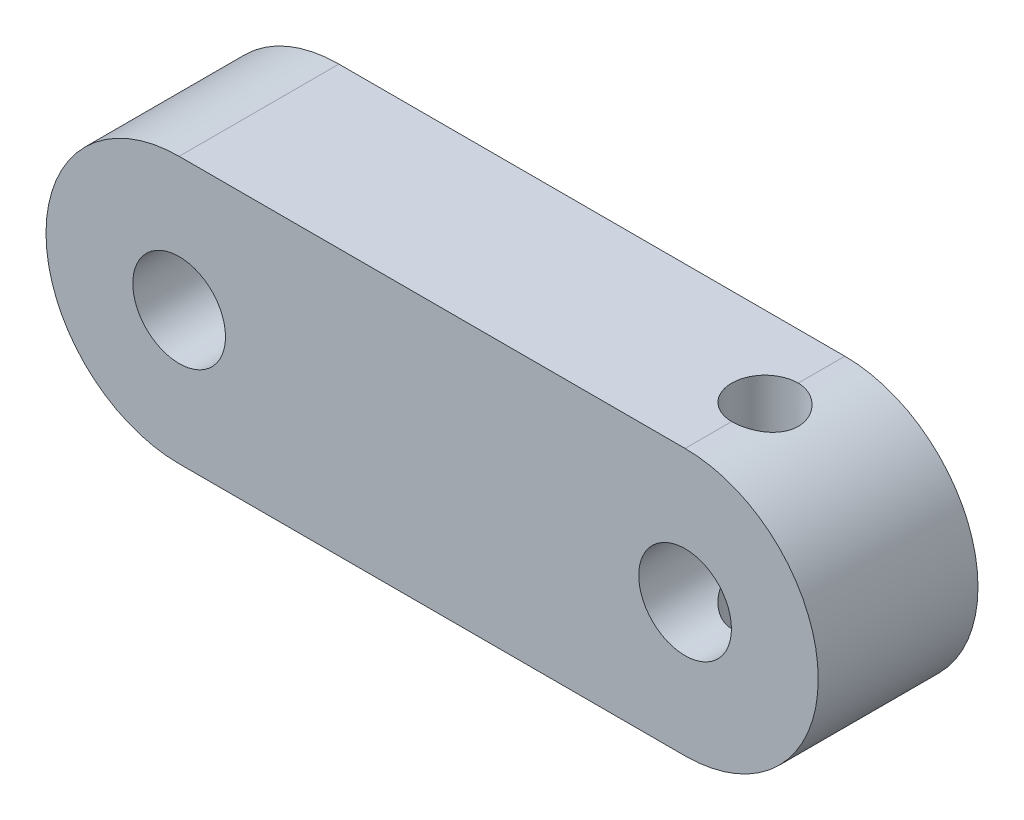
SolidWorks part; units mm, degrees
material "AISI 304"
ref_plane "Front Plane" through (0, 0, 0) normal (0, 0, 1) x (1, 0, 0)
ref_plane "Top Plane" through (0, 0, 0) normal (0, 1, 0) x (1, 0, 0)
ref_plane "Right Plane" through (0, 0, 0) normal (1, 0, 0) x (0, 0, -1)
sketch "Sketch1" plane through (0, 0, 0) normal (0, 0, 1) x (1, 0, 0)
  line L0 (-35.0425, 4.1934) -> (-16.0425, 4.1934)
  line L1 (-35.0425, -5.8066) -> (-16.0425, -5.8066)
  circle A0 centre (-35.0425, -0.8066) radius 1.7407
  circle A1 centre (-16.0425, -0.8066) radius 1.7407
  circle A2 centre (-16.0425, -0.8066) radius 5
  circle A3 centre (-35.0425, -0.8066) radius 5
  dimension "D1" = 19
extrude "Boss-Extrude1" add sketch "Sketch1" along normal blind 6 contours A3 A0 | A3 L1 A2 L0 | A2 A1
sketch "Sketch2" plane through (0, 4.1934, 0) normal (0, 1, 0) x (1, 0, 0)
  line L0 (-16.0425, -6) -> (-16.0425, 0) construction
  circle A0 centre (-16.0425, -3) radius 1.25
extrude "Cut-Extrude1" cut sketch "Sketch2" against normal through all
